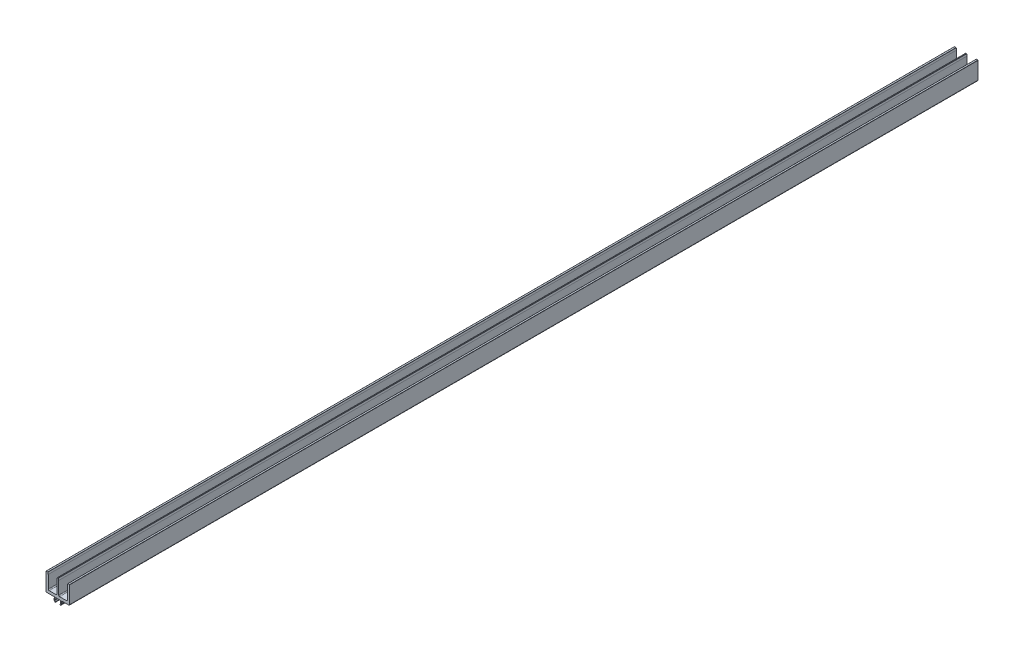
SolidWorks part; units mm, degrees
ref_plane "前视基准面" through (0, 0, 0) normal (0, 0, 1) x (1, 0, 0)
ref_plane "上视基准面" through (0, 0, 0) normal (0, 1, 0) x (1, 0, 0)
ref_plane "右视基准面" through (0, 0, 0) normal (1, 0, 0) x (0, 0, -1)
sketch "草图9" plane through (0, 0, 0) normal (0, 0, 1) x (1, 0, 0)
  line L0 (0, 14.0493) -> (0, -6.5713) construction
  line L1 (-1, 18) -> (-0.9974, 4)
  line L2 (10.9648, 19.8488) -> (10.5, 18)
  line L3 (-0.5353, 19.8485) -> (-1, 18)
  line L4 (0.5379, 19.8485) -> (1, 18)
  line L5 (-10.9621, 19.8485) -> (-10.5, 18)
  line L6 (3.7121, 0) -> (12, 0)
  line L7 (-2.2771, 0) -> (2.2771, 0)
  line L8 (-3.1904, -2.8) -> (-2.4975, -4)
  line L9 (-2.7695, -0.4132) -> (-3.1904, -2.8)
  line L10 (-3.7121, 0) -> (-4.1, -2.2)
  line L11 (-4.1, -2.2) -> (-4.3957, -2.7122)
  line L12 (-4.3957, -2.7122) -> (-3.3636, -4.5)
  line L13 (-12, 0) -> (-3.7121, 0)
  line L14 (-9.5, 3) -> (-1.9974, 3)
  line L15 (2, 3) -> (9.5, 3)
  line L16 (4.3957, -2.7122) -> (3.3636, -4.5)
  line L17 (3.1904, -2.8) -> (2.4975, -4)
  line L18 (12.8, 20) -> (11.1588, 20)
  line L19 (10.5, 4) -> (10.5, 18)
  line L20 (13, 1) -> (13, 19.8)
  line L21 (-0.3412, 20) -> (0.3438, 20)
  line L22 (1, 4) -> (1, 18)
  line L24 (-12.8, 20) -> (-11.1562, 20)
  line L25 (-10.5, 4) -> (-10.5, 18)
  line L26 (-13, 1) -> (-13, 19.8)
  line L27 (4.1, -2.2) -> (4.3957, -2.7122)
  line L28 (2.7695, -0.4132) -> (3.1904, -2.8)
  line L29 (3.7121, 0) -> (4.1, -2.2)
  arc A0 (11.1588, 20) -> (10.9648, 19.8488) centre (11.1588, 19.8) ccw
  arc A1 (0.5379, 19.8485) -> (0.3438, 20) centre (0.3438, 19.8) ccw
  arc A2 (-0.3412, 20) -> (-0.5353, 19.8485) centre (-0.3412, 19.8) ccw
  arc A3 (-10.9621, 19.8485) -> (-11.1562, 20) centre (-11.1562, 19.8) ccw
  arc A4 (2.7695, -0.4132) -> (2.2771, 0) centre (2.2771, -0.5) ccw
  arc A5 (-2.2771, 0) -> (-2.7695, -0.4132) centre (-2.2771, -0.5) ccw
  arc A6 (-10.5, 4) -> (-9.5, 3) centre (-9.5, 4) ccw
  arc A7 (1, 4) -> (2, 3) centre (2, 4) ccw
  arc A8 (9.5, 3) -> (10.5, 4) centre (9.5, 4) ccw
  arc A9 (2.4975, -4) -> (3.3636, -4.5) centre (2.9306, -4.25) ccw
  arc A10 (-3.3636, -4.5) -> (-2.4975, -4) centre (-2.9306, -4.25) ccw
  arc A11 (13, 19.8) -> (12.8, 20) centre (12.8, 19.8) ccw
  arc A12 (-12.8, 20) -> (-13, 19.8) centre (-12.8, 19.8) ccw
  arc A13 (-13, 1) -> (-12, 0) centre (-12, 1) ccw
  arc A14 (12, 0) -> (13, 1) centre (12, 1) ccw
  arc A15 (-1.9974, 3) -> (-0.9974, 4) centre (-1.9974, 4) ccw
extrude "拉伸1" add sketch "草图9" along normal mid plane 1000
